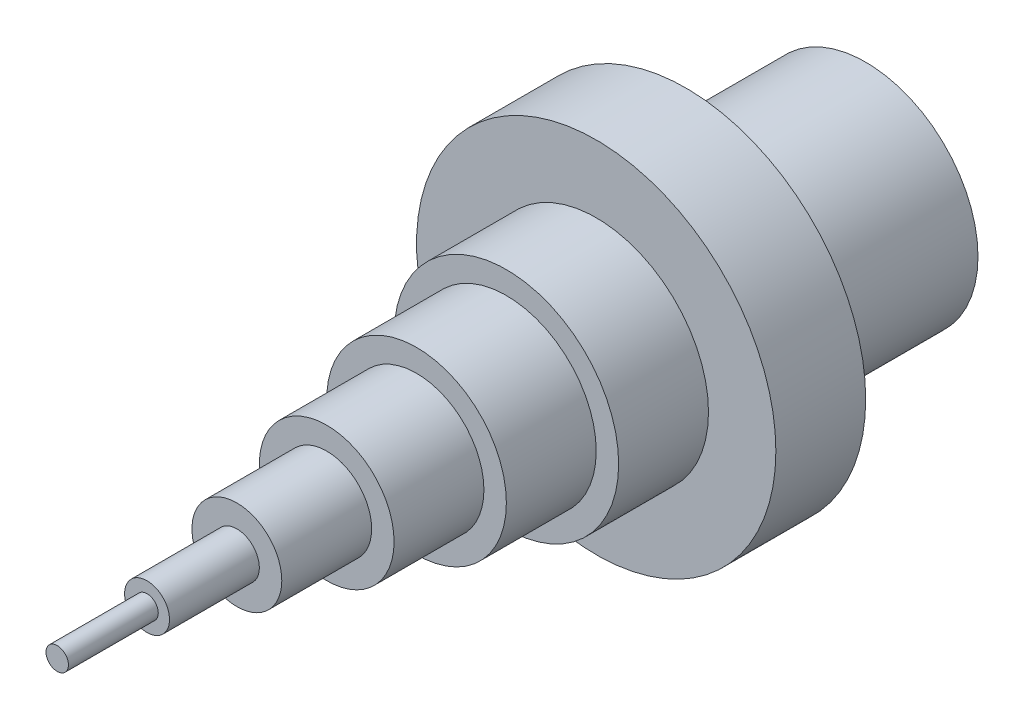
SolidWorks part; units mm, degrees
ref_plane "Front Plane" through (0, 0, 0) normal (0, 0, 1) x (1, 0, 0)
ref_plane "Top Plane" through (0, 0, 0) normal (0, 1, 0) x (1, 0, 0)
ref_plane "Right Plane" through (0, 0, 0) normal (1, 0, 0) x (0, 0, -1)
sketch "Sketch1" plane through (0, 0, 0) normal (0, 1, 0) x (1, 0, 0)
  line L0 (0, 0) -> (0, 186.9749) construction
  line L1 (0, 0) -> (2.5, 0)
  line L2 (2.5, 0) -> (2.5, 20)
  line L3 (2.5, 20) -> (5, 20)
  line L4 (5, 20) -> (5, 40)
  line L5 (5, 40) -> (10, 40)
  line L6 (10, 40) -> (10, 60)
  line L7 (10, 60) -> (15, 60)
  line L8 (15, 60) -> (15, 80)
  line L9 (15, 80) -> (20, 80)
  line L10 (20, 80) -> (20, 100)
  line L11 (20, 100) -> (25, 100)
  line L12 (25, 100) -> (25, 120)
  line L13 (25, 120) -> (40, 120)
  line L14 (40, 120) -> (40, 140)
  line L15 (40, 140) -> (25, 140)
  line L16 (25, 140) -> (25, 180)
  line L17 (25, 180) -> (0, 180)
  line L18 (0, 180) -> (0, 0)
  dimension "D1" = 180
  dimension "D2" = 20
  dimension "D3" = 50
  dimension "D4" = 80
  dimension "D5" = 50
  dimension "D6" = 40
  dimension "D7" = 30
  dimension "D8" = 20
  dimension "D9" = 10
  dimension "D10" = 5
revolve "Revolve1" add sketch "Sketch1" angle 360 about L0
sketch "Sketch3" plane through (0, 0, -180) normal (0, 0, -1) x (-1, 0, 0)
  circle A0 centre (0, 0) radius 20
  dimension "D1" = 40
extrude "Cut-Extrude1" cut sketch "Sketch3" against normal blind 40
